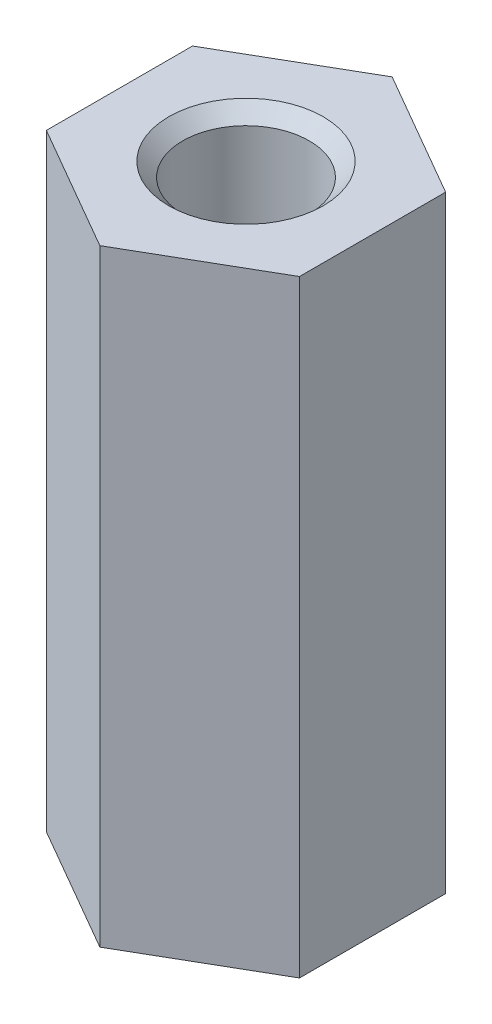
SolidWorks part; units mm, degrees
material "6061 Alloy"
ref_plane "Front Plane" through (0, 0, 0) normal (0, 0, 1) x (1, 0, 0)
ref_plane "Top Plane" through (0, 0, 0) normal (0, 1, 0) x (1, 0, 0)
ref_plane "Right Plane" through (0, 0, 0) normal (1, 0, 0) x (0, 0, -1)
sketch "Sketch1" plane through (0, 0, 0) normal (0, 1, 0) x (1, 0, 0)
  line L1 (-2.5, 1.4434) -> (-2.5, -1.4434)
  line L2 (-2.5, -1.4434) -> (0, -2.8868)
  line L3 (0, -2.8868) -> (2.5, -1.4434)
  line L4 (2.5, -1.4434) -> (2.5, 1.4434)
  line L5 (2.5, 1.4434) -> (0, 2.8868)
  line L6 (0, 2.8868) -> (-2.5, 1.4434)
  circle A0 centre (0, 0) radius 2.5 construction
  dimension "D1" = 5
extrude "Boss-Extrude1" add sketch "Sketch1" along normal blind 12
hole_wizard "M3 Tapped Hole1" positions "Sketch2" profile "Sketch3" tap size "M3" standard "ISO"
sketch "Sketch2" plane through (0, 12, 0) normal (0, 1, 0) x (1, 0, 0)
  point P0 (0, 0)
sketch "Sketch3" plane through (0, 12, 0) normal (1, 0, 0) x (0, 0, 1)
  line L0 (0, 0) -> (0, 8.2511)
  line L1 (0, 8.2511) -> (1.25, 7.5)
  line L2 (1.25, 7.5) -> (1.25, 0.275)
  line L3 (1.25, 0.275) -> (1.525, 0)
  line L5 (1.525, 0) -> (0, 0)
  line L6 (-1.25, 0.275) -> (-1.525, 0) construction
  line L10 (0, 8.2511) -> (-1.25, 7.5) construction
  line L11 (0, -6.35) -> (0, 107.95) construction
  dimension "Tap Drill Dia." = 2.5
  dimension "Tap Drill Depth" = 7.5
  dimension "Near C'Sink Dia." = 3.05
  dimension "Near C'Sink Angle" = 90
  dimension "Drill Angle" = 118
cosmetic thread "Hole Thread1" parameters "D1"=6, "D2"=3
hole_wizard "M3 Tapped Hole2" positions "Sketch4" profile "Sketch5" tap size "M3" standard "ISO"
sketch "Sketch4" plane through (0, 0, 0) normal (0, -1, 0) x (-1, 0, 0)
  point P0 (0, 0)
sketch "Sketch5" plane through (0, 0, 0) normal (1, 0, 0) x (0, 0, -1)
  line L0 (0, 0) -> (0, 8.2511)
  line L1 (0, 8.2511) -> (1.25, 7.5)
  line L2 (1.25, 7.5) -> (1.25, 0.275)
  line L3 (1.25, 0.275) -> (1.525, 0)
  line L5 (1.525, 0) -> (0, 0)
  line L6 (-1.25, 0.275) -> (-1.525, 0) construction
  line L10 (0, 8.2511) -> (-1.25, 7.5) construction
  line L11 (0, -6.35) -> (0, 107.95) construction
  dimension "Tap Drill Dia." = 2.5
  dimension "Tap Drill Depth" = 7.5
  dimension "Near C'Sink Dia." = 3.05
  dimension "Near C'Sink Angle" = 90
  dimension "Drill Angle" = 118
cosmetic thread "Hole Thread2" parameters "D1"=6, "D2"=3
